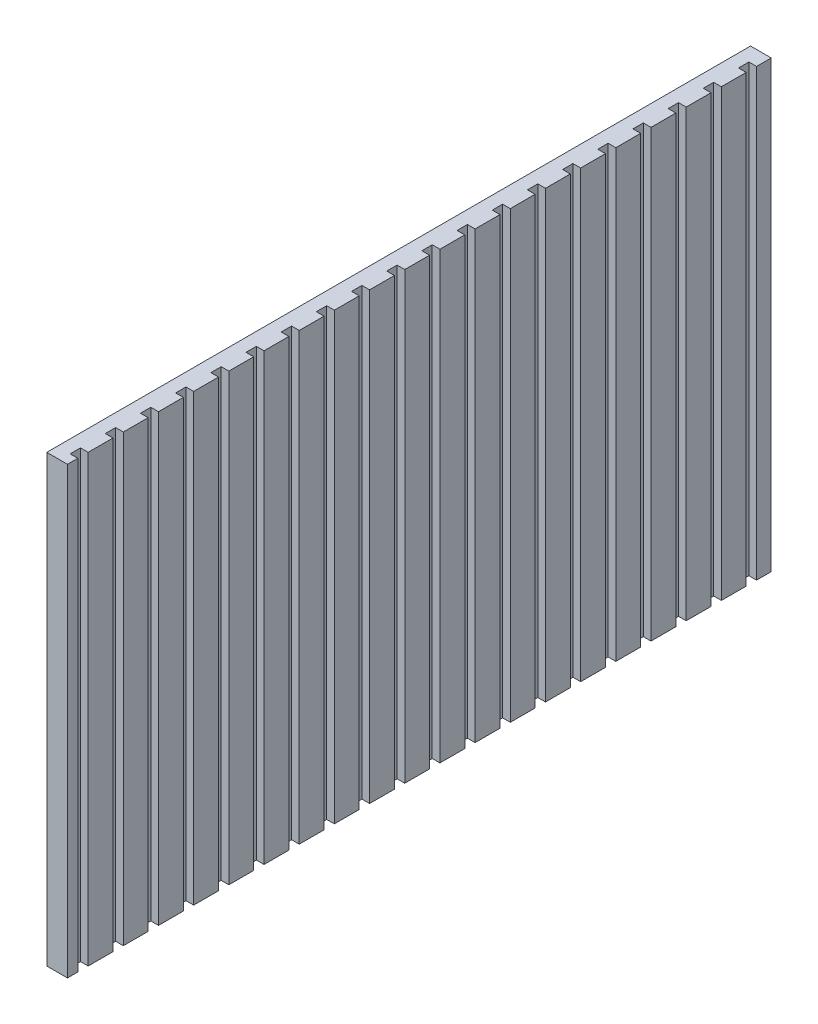
SolidWorks part; units mm, degrees
material "Free-Cutting Brass, UNS C36000"
ref_plane "Front Plane" through (0, 0, 0) normal (0, 0, 1) x (1, 0, 0)
ref_plane "Top Plane" through (0, 0, 0) normal (0, 1, 0) x (1, 0, 0)
ref_plane "Right Plane" through (0, 0, 0) normal (1, 0, 0) x (0, 0, -1)
sketch "Sketch1" plane through (0, 0, 0) normal (1, 0, 0) x (0, 0, -1)
  line L1 (-170.05, -107.5) -> (170.05, -107.5)
  line L2 (-170.05, -107.5) -> (-170.05, 107.5)
  line L3 (-170.05, 107.5) -> (170.05, 107.5)
  line L4 (170.05, -107.5) -> (170.05, 107.5)
  line L5 (-170.05, -107.5) -> (170.05, 107.5) construction
  line L6 (-170.05, 107.5) -> (170.05, -107.5) construction
  point P0 (0, 0)
  dimension "D1" = 340.1
  dimension "D2" = 215
extrude "Boss-Extrude1" add sketch "Sketch1" along normal blind 10
sketch "Sketch2" plane through (0, 107.5, 0) normal (0, 1, 0) x (1, 0, 0)
  line L0 (10, 170.05) -> (10, -170.05) construction
  line L1 (6.2819, -165.05) -> (13.7181, -165.05)
  line L2 (6.2819, -165.05) -> (6.2819, -160.05)
  line L3 (6.2819, -160.05) -> (13.7181, -160.05)
  line L4 (13.7181, -165.05) -> (13.7181, -160.05)
  line L5 (6.2819, -165.05) -> (13.7181, -160.05) construction
  line L6 (6.2819, -160.05) -> (13.7181, -165.05) construction
  line L7 (10, -170.05) -> (0, -170.05) construction
  point P0 (10, -162.55)
  dimension "D1" = 5
  dimension "D2" = 5
extrude "Cut-Extrude1" cut sketch "Sketch2" against normal through all
pattern_linear "LPattern1" count 20 spacing 17 along (0, 0, -1) of "Cut-Extrude1"
